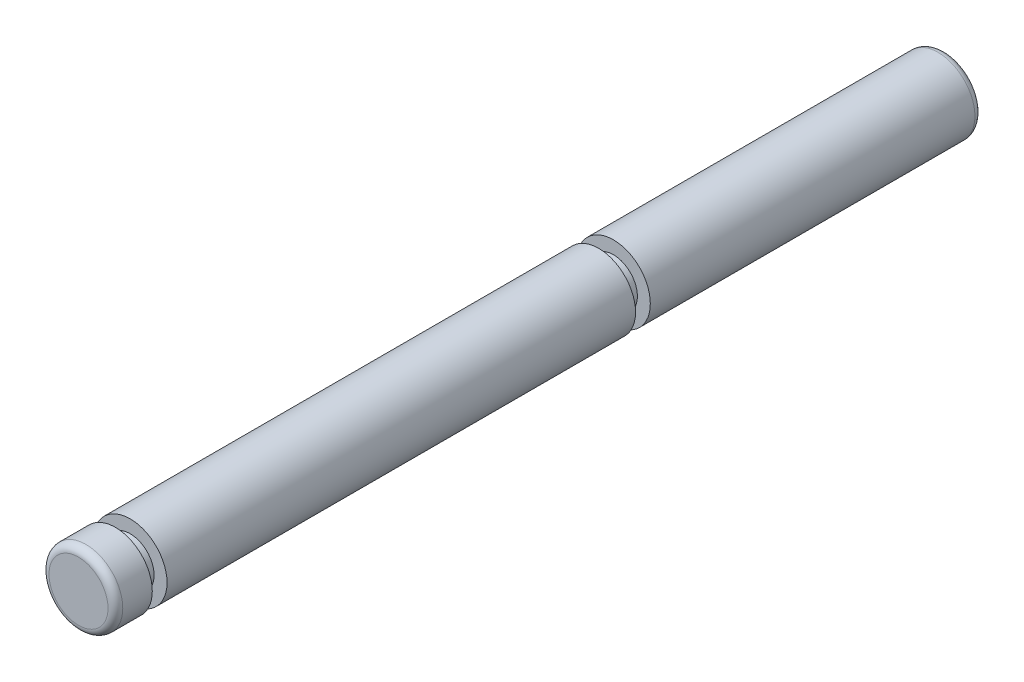
SolidWorks part; units mm, degrees
ref_plane "Plan de face" through (0, 0, 0) normal (0, 0, 1) x (1, 0, 0)
ref_plane "Plan de dessus" through (0, 0, 0) normal (0, 1, 0) x (1, 0, 0)
ref_plane "Plan de droite" through (0, 0, 0) normal (1, 0, 0) x (0, 0, -1)
sketch "Esquisse1" plane through (0, 0, 0) normal (1, 0, 0) x (0, 0, -1)
  line L0 (0, 0) -> (0, 0.8)
  line L1 (-0.2, 1) -> (-9, 1)
  line L2 (-23.5, 0.8) -> (-23.5, 0)
  line L3 (-23.5, 0) -> (0, 0)
  line L4 (-22.5, 1) -> (-23.3, 1)
  line L5 (-1000, 0) -> (49000, 0) construction
  line L6 (-22.5, 1) -> (-22.5, 0.65)
  line L7 (-22.5, 0.65) -> (-22.1, 0.65)
  line L8 (-22.1, 1) -> (-22.1, 0.65)
  line L9 (-9.4, 1) -> (-9.4, 0.65)
  line L10 (-9.4, 0.65) -> (-9, 0.65)
  line L11 (-9, 0.65) -> (-9, 1)
  line L12 (-9.4, 1) -> (-22.1, 1)
  arc A0 (-23.3, 1) -> (-23.5, 0.8) centre (-23.3, 0.8) ccw
  arc A1 (0, 0.8) -> (-0.2, 1) centre (-0.2, 0.8) ccw
  point P13 (0, 1)
  dimension "D6" = 0.2
  dimension "D7" = 0.2
  dimension "D1" = 23.5
  dimension "D2" = 1
  dimension "D3" = 1.3
  dimension "D4" = 0.4
  dimension "D5" = 1
  dimension "D8" = 14.1
  dimension "D9" = 0.4
revolve "Révolution1" add sketch "Esquisse1" angle 360 about L3
